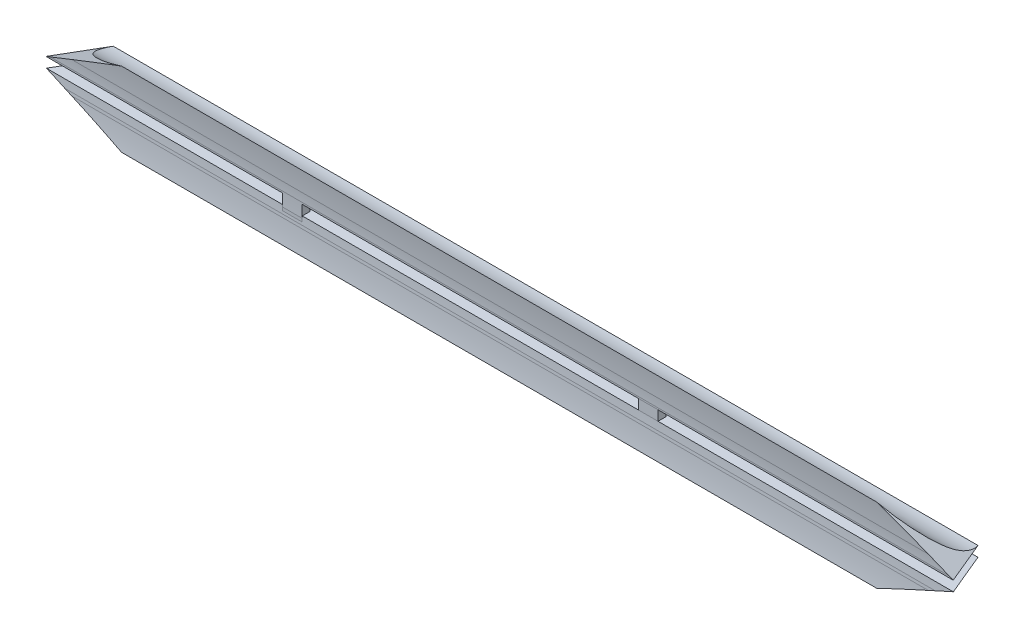
SolidWorks part; units mm, degrees
ref_plane "Front Plane" through (0, 0, 0) normal (0, 0, 1) x (1, 0, 0)
ref_plane "Top Plane" through (0, 0, 0) normal (0, 1, 0) x (1, 0, 0)
ref_plane "Right Plane" through (0, 0, 0) normal (1, 0, 0) x (0, 0, -1)
sketch "Sketch1" plane through (0, 0, 0) normal (0, 1, 0) x (1, 0, 0)
  line L0 (0, 0) -> (88.9, 142.24)
  line L1 (88.9, 142.24) -> (241.3, 142.24)
  line L2 (241.3, 142.24) -> (304.8, 0)
  line L4 (0, 0) -> (113.03, 0)
  line L5 (113.03, 0) -> (113.03, -8.89)
  line L6 (113.03, -8.89) -> (151.13, -8.89)
  line L7 (151.13, -8.89) -> (151.13, 0)
  line L8 (151.13, 0) -> (304.8, 0)
  dimension "D1" = 142.24
  dimension "D2" = 304.8
  dimension "D3" = 152.4
  dimension "D4" = 88.9
  dimension "D5" = 8.89
  dimension "D6" = 38.1
  dimension "D7" = 153.67
  dimension "D8" = 142.24
extrude "Boss-Extrude1" add sketch "Sketch1" along normal blind 3.302
chamfer "Chamfer1" distance 1.27 angle 65 6 edges at (273.05, 0, -71.12) (165.1, 0, -142.24) (44.45, 0, -71.12) (273.05, 3.302, -71.12) (165.1, 3.302, -142.24) (44.45, 3.302, -71.12)
sketch "Sketch7" plane through (0, 3.302, 0) normal (0, 1, 0) x (1, 0, 0)
  line L0 (113.03, -4.318) -> (151.13, -4.318) construction
  line L1 (113.03, 0) -> (113.03, -8.89) construction
  line L2 (151.13, -8.89) -> (151.13, 0) construction
  dimension "D1" = 4.318
sketch "Sketch2" plane through (0, 0, 0) normal (1, 0, 0) x (0, 0, -1)
  line L1 (-8.89, 1.651) -> (20.2175, 1.651) construction
  line L2 (0, 0) -> (139.5165, 0) construction
  line L3 (0, 0) -> (13.712, 0)
  line L4 (-8.89, 3.302) -> (-8.89, 0) construction
  line L5 (0, 3.302) -> (13.712, 3.302)
  arc A0 (-43.0515, -66.1518) -> (-64.5848, 81.0742) centre (-78.1629, 3.9005) ccw
  spline S0 degree 3 poles (13.712, 0) (11.0209, -0.0927) (7.3046, -1.1015) (2.0711, -5.2898) (-0.2796, -8.5973) (-1.3194, -11.4365) knots 0 0 0 0 0.405372 0.550927 1 1 1 1
  spline S1 degree 3 poles (-1.3194, -11.4365) (-0.62, -7.6658) (0.0417, -3.8485) (0, 0) knots 0 0 0 0 1 1 1 1
  spline S2 degree 3 poles (-1.3194, 14.7385) (-0.62, 10.9678) (0.0417, 7.1505) (0, 3.302) knots 0 0 0 0 1 1 1 1
  spline S3 degree 3 poles (13.712, 3.302) (11.0209, 3.3947) (7.3046, 4.4035) (2.0711, 8.5918) (-0.2796, 11.8993) (-1.3194, 14.7385) knots 0 0 0 0 0.405372 0.550927 1 1 1 1
  dimension "D1" = 78.359
extrude "Boss-Extrude2" add sketch "Sketch2" along normal blind 304.8 contours S1 S0 L3 A0
sketch "Sketch3" plane through (0, 0, 0) normal (1, 0, 0) x (0, 0, -1)
  line L0 (0, 23.3434) -> (0, -21.4717) construction
ref_plane "Plane1" through (0, 0, 0) normal (-0.5039, 0, 0.8638) x (0, -1, 0)
sketch "Sketch4" plane through (0, 0, 0) normal (-0.5039, 0, 0.8638) x (0, -1, 0)
  line L0 (-1.651, 0) -> (-1.651, 11.9934) construction
  line L1 (0, -7.4611) -> (0, 8.059)
  line L2 (0, 8.059) -> (11.6905, 33.1293)
  line L4 (11.6905, 33.1293) -> (11.6905, -6.2846)
  line L5 (11.6905, -6.2846) -> (0, -7.4611)
  line L6 (-23.3434, 0) -> (21.4717, 0) construction
  line L11 (-2.032, 0) -> (-1.27, 0) construction
  line L12 (-14.9925, 33.1293) -> (-14.9925, -6.2846)
  line L14 (-3.302, -7.4611) -> (-3.302, 8.059)
  line L15 (-14.9925, -6.2846) -> (-3.302, -7.4611)
  line L17 (-3.302, 2.7742) -> (-3.302, 0) construction
  line L18 (-14.9925, 33.1293) -> (-3.302, 8.059)
  dimension "D1" = 65
extrude "Leading Side" cut sketch "Sketch4" against normal through all both and the other way through all contours L12 L15 L14 L18 | L5 L1 L2 L4
ref_plane "Plane2" through (304.8, 0, 0) normal (1, 0, 0) x (0, 0, -1)
sketch "Sketch5" plane through (304.8, 0, 0) normal (1, 0, 0) x (0, 0, -1)
  line L0 (0, 22.7644) -> (0, -16.1192) construction
  line L1 (0, 23.3434) -> (0, -21.4717) construction
ref_plane "Plane3" through (45.0893, 0, 108.2135) normal (-0.3846, 0, -0.9231) x (0, -1, 0)
sketch "Sketch6" plane through (45.0893, 0, 108.2135) normal (-0.3846, 0, -0.9231) x (0, -1, 0)
  line L0 (0, -286.6274) -> (0, -278.5989)
  line L1 (0, -278.5989) -> (11.4365, -254.0733)
  line L2 (11.4365, -280.8461) -> (11.4365, -33.6034) construction
  line L3 (11.4365, -254.0733) -> (11.4365, -287.9656)
  line L4 (11.4365, -287.9656) -> (0, -286.6274)
  line L5 (-22.7644, -281.3536) -> (16.1192, -281.3536) construction
  line L6 (-1.651, -136.6657) -> (-1.651, -278.2497) construction
  line L7 (-14.7385, -254.0733) -> (-14.7385, -287.9656)
  line L8 (-3.302, -278.6004) -> (-14.7385, -254.0733)
  line L9 (-3.302, -286.6274) -> (-3.302, -278.6004)
  line L10 (-14.7385, -287.9656) -> (-3.302, -286.6274)
  line L11 (0, -286.6274) -> (0, -278.2237) construction
  dimension "D1" = 65
extrude "Trailing Side" cut sketch "Sketch6" along normal blind 254 and the other way blind 27.94
sketch "Sketch8" plane through (0, 0, 0) normal (0, 1, 0) x (1, 0, 0)
  line L0 (200.2174, -1.3194) -> (200.2174, 156.1436) construction
  line L1 (275.7961, -1.3194) -> (36.9535, -1.3194) construction
  dimension "D1" = 101.6
sketch "Sketch9" plane through (0, 0, 0) normal (0, 0, 1) x (1, 0, 0)
  line L1 (-0.4873, 0) -> (305.0063, 0)
  line L2 (-0.4873, 0) -> (-0.4873, 3.302)
  line L3 (-0.4873, 3.302) -> (305.0063, 3.302)
  line L4 (305.0063, 0) -> (305.0063, 3.302)
  point P4 (-0.4873, 3.302)
extrude "Cut-Extrude1" cut sketch "Sketch9" against normal through all both and the other way through all
sketch "Sketch10" plane through (0, 0, 0) normal (0, 1, 0) x (1, 0, 0)
  line L0 (200.2174, 0.099) -> (206.5674, 0.099)
  line L2 (206.5674, 0.099) -> (206.5674, 2.639)
  line L3 (206.5674, 2.639) -> (200.2174, 2.639)
  line L4 (200.2174, -1.3194) -> (200.2174, 156.1436) construction
  line L5 (200.2174, 2.639) -> (200.2174, 0.099)
  line L6 (301.7745, 0.099) -> (9.3877, 0.099) construction
  dimension "D1" = 6.35
  dimension "D2" = 2.54
  dimension "D3" = 0
extrude "Boss-Extrude3" add sketch "Sketch10" along normal up to next
sketch "Sketch11" plane through (0, 3.302, 0) normal (0, -1, 0) x (1, 0, 0)
  line L0 (9.3299, 0) -> (301.8174, 0) construction
  line L1 (91.8799, 0) -> (85.5299, 0)
  line L2 (91.8799, 0) -> (91.8799, -2.54)
  line L3 (91.8799, -2.54) -> (85.5299, -2.54)
  line L4 (85.5299, 0) -> (85.5299, -2.54)
  dimension "D1" = 2.54
  dimension "D2" = 6.35
  dimension "D3" = 76.2
extrude "Boss-Extrude4" add sketch "Sketch11" along normal up to next
sketch "Sketch12" plane through (0, 0, 0) normal (1, 0, 0) x (0, 0, -1)
  circle A0 centre (-78.5778, 1.651) radius 78.6099
extrude "Cut-Extrude3" cut sketch "Sketch12" along normal through all
